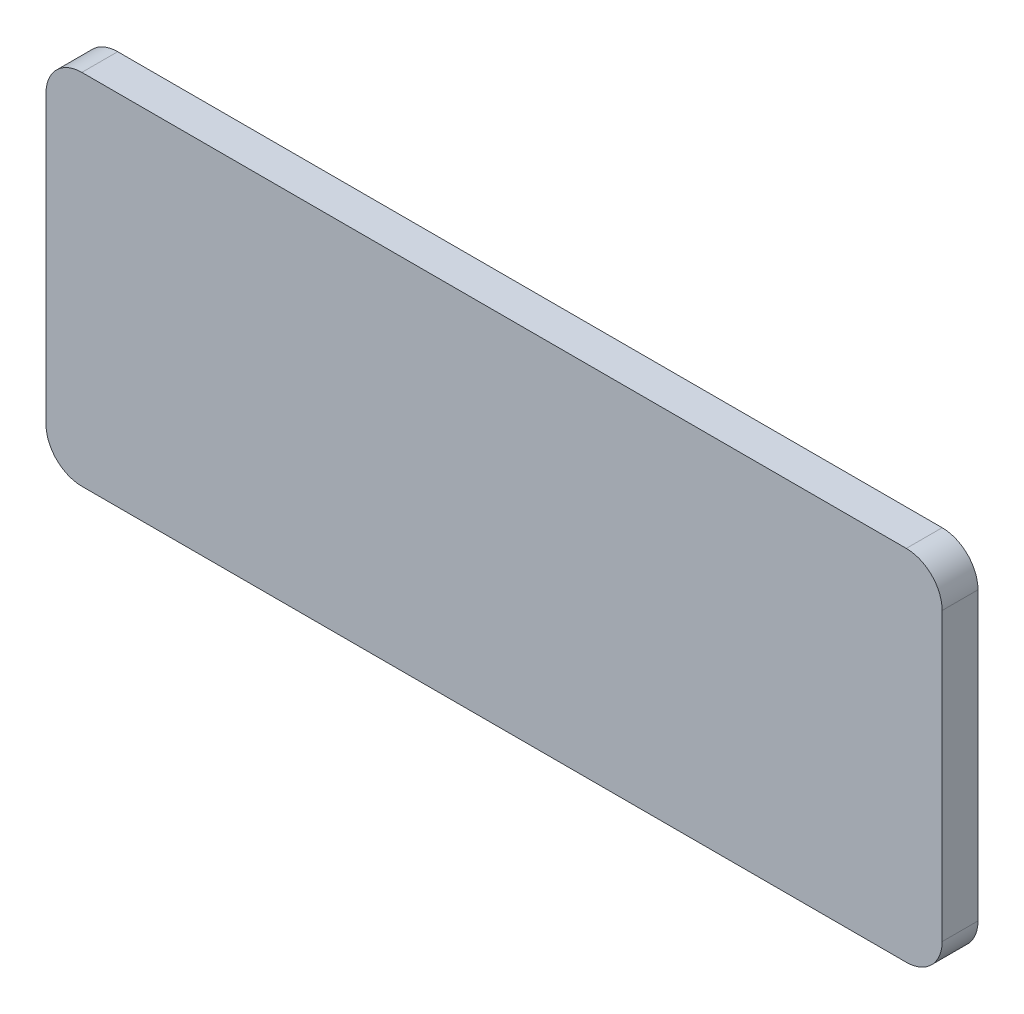
SolidWorks part; units mm, degrees
material "Plastique personnalisé"
ref_plane "Plan de face" through (0, 0, 0) normal (0, 0, 1) x (1, 0, 0)
ref_plane "Plan de dessus" through (0, 0, 0) normal (0, 1, 0) x (1, 0, 0)
ref_plane "Plan de droite" through (0, 0, 0) normal (1, 0, 0) x (0, 0, -1)
sketch "Esquisse1" plane through (0, 0, 0) normal (0, 0, 1) x (1, 0, 0)
  line L1 (-25, -10) -> (25, -10)
  line L2 (-25, -10) -> (-25, 10)
  line L3 (-25, 10) -> (25, 10)
  line L4 (25, -10) -> (25, 10)
  line L5 (-25, -10) -> (25, 10) construction
  line L6 (-25, 10) -> (25, -10) construction
  point P0 (0, 0)
  dimension "D1" = 50
  dimension "D2" = 20
extrude "Boss.-Extru.1" add sketch "Esquisse1" along normal blind 2
fillet "Congé1" radius 2 4 edges at (-25, -10, 1) (-25, 10, 1) (25, -10, 1) (25, 10, 1)
